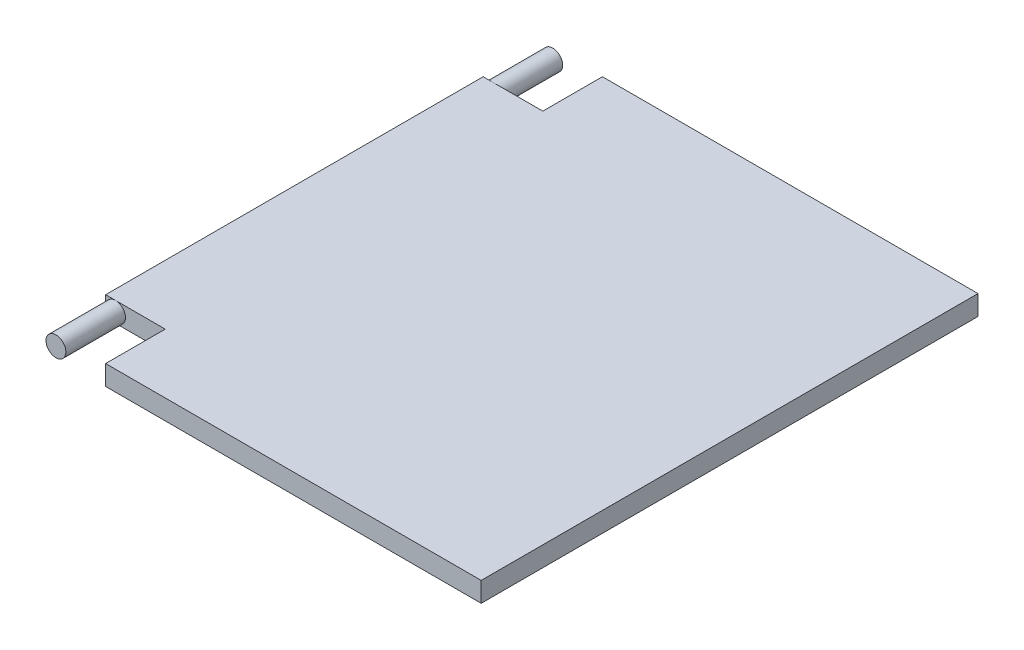
SolidWorks part; units mm, degrees
ref_plane "Plan de face" through (0, 0, 0) normal (0, 0, 1) x (1, 0, 0)
ref_plane "Plan de dessus" through (0, 0, 0) normal (0, 1, 0) x (1, 0, 0)
ref_plane "Plan de droite" through (0, 0, 0) normal (1, 0, 0) x (0, 0, -1)
sketch "Esquisse1" plane through (0, 0, 0) normal (0, 1, 0) x (1, 0, 0)
  line L0 (0, 0) -> (189, 0)
  line L1 (189, 0) -> (189, 250)
  line L2 (189, 250) -> (0, 250)
  line L3 (0, 250) -> (0, 220)
  line L4 (0, 220) -> (-30, 220)
  line L5 (-30, 220) -> (-30, 30)
  line L6 (-30, 30) -> (0, 30)
  line L7 (0, 30) -> (0, 0)
  dimension "D1" = 189
  dimension "D2" = 250
  dimension "D3" = 30
  dimension "D4" = 30
  dimension "D5" = 30
extrude "Boss.-Extru.1" add sketch "Esquisse1" along normal blind 10
sketch "Esquisse2" plane through (0, 0, -30) normal (0, 0, 1) x (1, 0, 0)
  line L0 (-30, 10) -> (0, 10) construction
  line L1 (-30, 0) -> (0, 0) construction
  line L2 (-30, 10) -> (-30, 0) construction
  circle A0 centre (-25, 5) radius 5
extrude "Boss.-Extru.2" add sketch "Esquisse2" along normal blind 30
sketch "Esquisse3" plane through (0, 0, -220) normal (0, 0, -1) x (-1, 0, 0)
  line L0 (0, 0) -> (30, 0) construction
  line L1 (0, 10) -> (30, 10) construction
  line L2 (30, 10) -> (30, 0) construction
  circle A0 centre (25, 5) radius 5
extrude "Boss.-Extru.3" add sketch "Esquisse3" along normal blind 30
